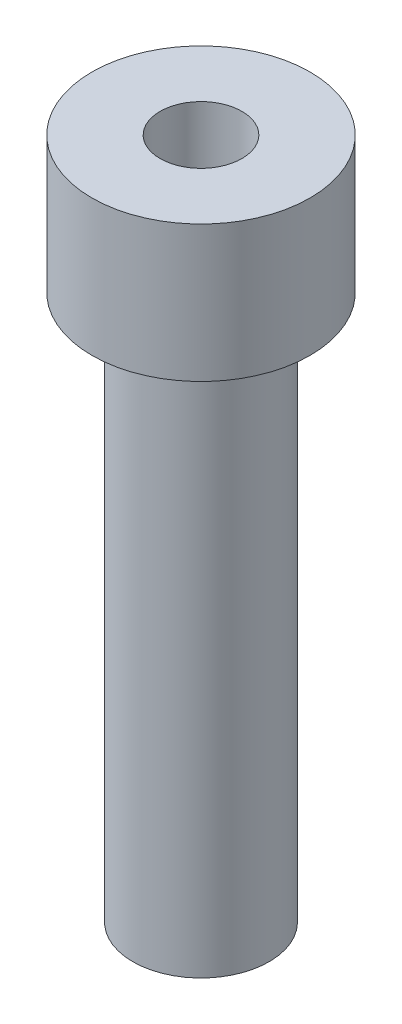
SolidWorks part; units mm, degrees
ref_plane "Front Plane" through (0, 0, 0) normal (0, 0, 1) x (1, 0, 0)
ref_plane "Top Plane" through (0, 0, 0) normal (0, 1, 0) x (1, 0, 0)
ref_plane "Right Plane" through (0, 0, 0) normal (1, 0, 0) x (0, 0, -1)
sketch "Sketch1" plane through (0, 0, 0) normal (0, 1, 0) x (1, 0, 0)
  circle A0 centre (0, 0) radius 2.5
  dimension "D1" = 5
extrude "Boss-Extrude1" add sketch "Sketch1" along normal blind 20
sketch "Sketch2" plane through (0, 20, 0) normal (0, 1, 0) x (1, 0, 0)
  circle A0 centre (0, 0) radius 4
  dimension "D1" = 8
extrude "Boss-Extrude2" add sketch "Sketch2" along normal blind 5
sketch "Sketch3" plane through (0, 25, 0) normal (0, 1, 0) x (1, 0, 0)
  circle A0 centre (0, 0) radius 1.5
  dimension "D1" = 3
extrude "Cut-Extrude1" cut sketch "Sketch3" against normal blind 3 contours A0
